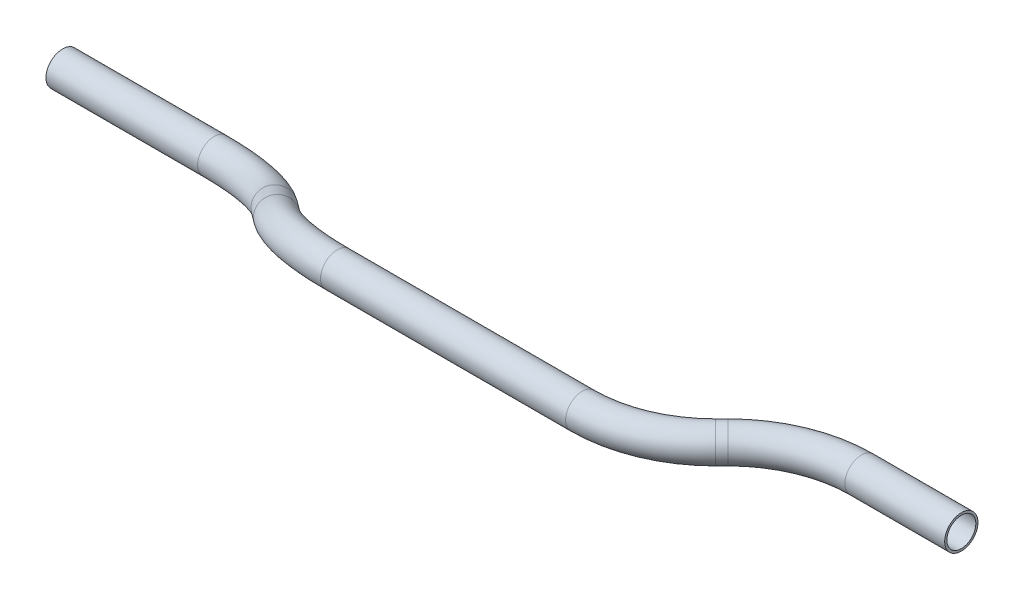
SolidWorks part; units mm, degrees
ref_plane "Front Plane" through (0, 0, 0) normal (0, 0, 1) x (1, 0, 0)
ref_plane "Top Plane" through (0, 0, 0) normal (0, 1, 0) x (1, 0, 0)
ref_plane "Right Plane" through (0, 0, 0) normal (1, 0, 0) x (0, 0, -1)
sketch3d "3DSketch2"
  line L0 (0, 0, 0) -> (86.6756, 0, 0)
  line L1 (0, 27.2535, 0) -> (0, 27.2535, 48.26) construction
  line L2 (0, 27.2535, 48.26) -> (467.4369, 27.2535, 48.26) construction
  line L3 (140.5571, 10.9747, 19.4337) -> (151.3439, 16.2789, 28.8263)
  line L4 (456.6854, 27.2535, 0) -> (513.7758, 27.2535, 0)
  line L5 (0, 0, 0) -> (0, 27.2535, 0) construction
  line L6 (0, 27.2535, 0) -> (467.4369, 27.2535, 0) construction
  line L7 (205.2254, 27.2535, 48.26) -> (345.2992, 27.2535, 48.26)
  line L8 (399.1808, 27.2535, 25.9415) -> (402.8039, 27.2535, 22.3185)
  arc A0 (402.8039, 27.2535, 22.3185) -> (456.6854, 27.2535, 0) centre (456.6854, 27.2535, 76.2) ccw
  arc A1 (345.2992, 27.2535, 48.26) -> (399.1808, 27.2535, 25.9415) centre (345.2992, 27.2535, -27.94) ccw
  arc A2 (151.3439, 16.2789, 28.8263) -> (205.2254, 27.2535, 48.26) centre (205.2254, -10.2164, -18.0909) ccw
  arc A3 (86.6756, 0, 0) -> (140.5571, 10.9747, 19.4337) centre (86.6756, 37.4699, 66.3509) ccw
  point P7 (425.1223, 27.2535, 0)
  point P9 (456.6854, -48.9465, 76.2)
  point P12 (376.8623, 27.2535, 48.26)
  point P14 (345.2992, 103.4535, -27.94)
  point P17 (173.6623, 27.2535, 48.26)
  point P19 (205.2254, 56.1346, -55.5608)
  point P22 (118.2387, 0, 0)
  point P26 (86.6756, -28.881, 103.8208)
  dimension "D5" = 203.2
  dimension "D10" = 27.2535
  dimension "D7" = 76.2
  dimension "D1" = 118.2387
  dimension "D2" = 48.26
  dimension "D3" = 45
  dimension "D4" = 135
  dimension "D6" = 88.6535
  dimension "D11" = 467.4369
ref_plane "Plane1" through (0, 0, 0) normal (1, 0, 0) x (0, 0, -1)
sketch "Sketch1" plane through (0, 0, 0) normal (1, 0, 0) x (0, 0, -1)
  circle A0 centre (0, 0) radius 9.525
  circle A1 centre (0, 0) radius 8.2804
  dimension "D1" = 19.05
  dimension "D2" = 1.2446
sweep "Sweep2" add profiles "Sketch1" path "3DSketch2"
